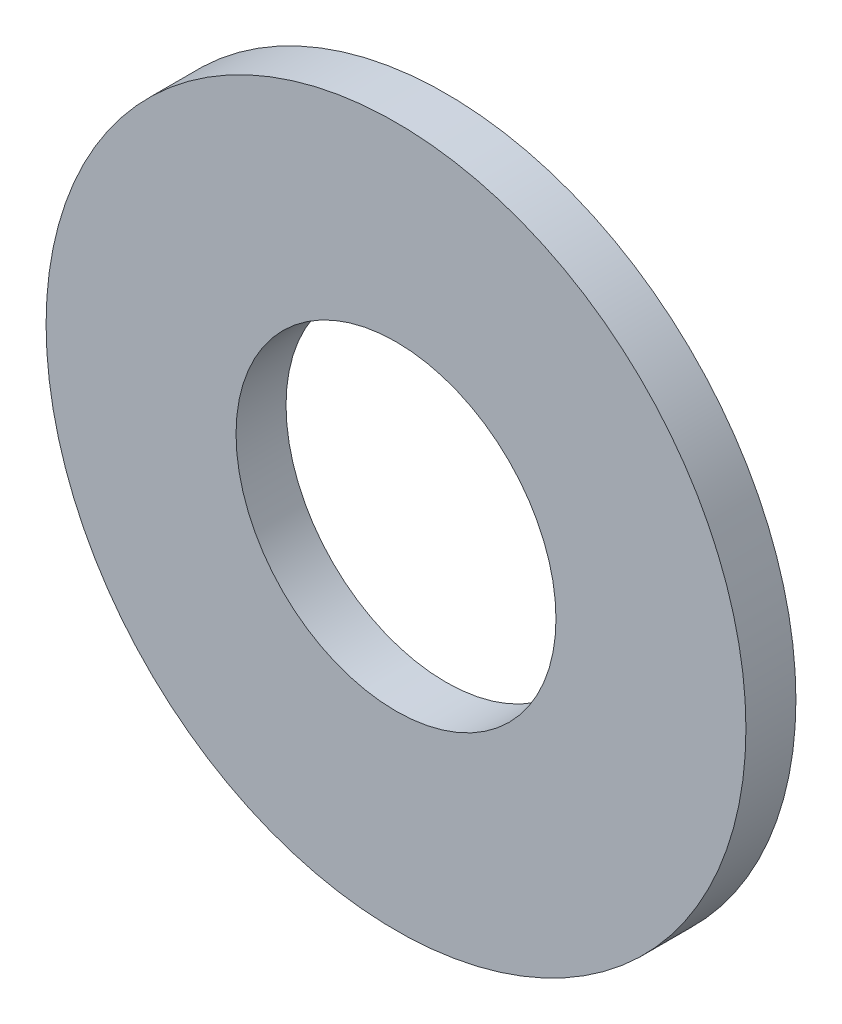
SolidWorks part; units mm, degrees
material "AISI Тип A2 Инструментальная сталь"
ref_plane "Front" through (0, 0, 0) normal (0, 0, 1) x (1, 0, 0)
ref_plane "Top" through (0, 0, 0) normal (0, 1, 0) x (1, 0, 0)
ref_plane "Right" through (0, 0, 0) normal (1, 0, 0) x (0, 0, -1)
sketch "Эскиз1" plane through (0, 0, 0) normal (0, 0, 1) x (1, 0, 0)
  circle A0 centre (0, 0) radius 3.5
  circle A1 centre (0, 0) radius 1.6
  dimension "D1" = 7
  dimension "D2" = 3.2
extrude "Бобышка-Вытянуть1" add sketch "Эскиз1" along normal blind 0.5
